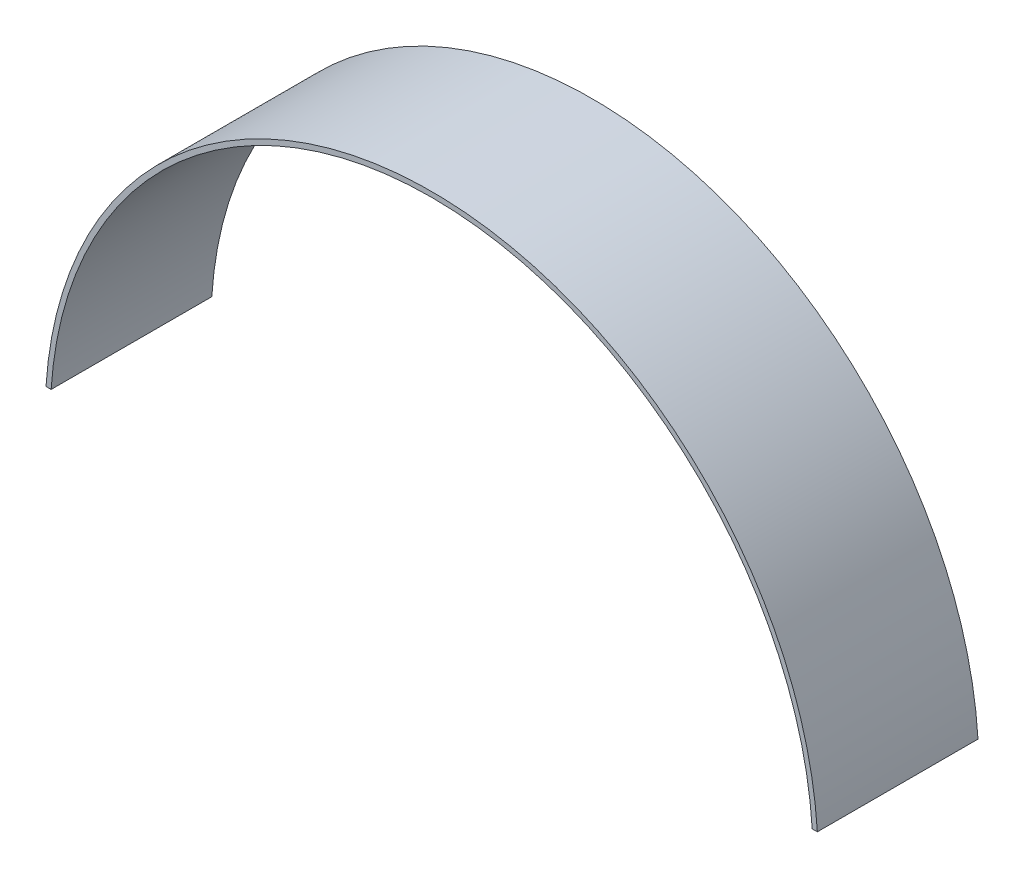
SolidWorks part; units mm, degrees
ref_plane "Front Plane" through (0, 0, 0) normal (0, 0, 1) x (1, 0, 0)
ref_plane "Top Plane" through (0, 0, 0) normal (0, 1, 0) x (1, 0, 0)
ref_plane "Right Plane" through (0, 0, 0) normal (1, 0, 0) x (0, 0, -1)
sketch "Sketch1" plane through (0, 0, 0) normal (0, 0, 1) x (1, 0, 0)
  line L1 (-90.1815, 4.6108) -> (-72.285, 4.6108)
  line L2 (-72.285, 4.6108) -> (-71.0625, 4.6108)
  line L3 (71.0625, 4.6108) -> (90.1815, 4.6108)
  arc A0 (90.1815, 4.6108) -> (-90.1815, 4.6108) centre (0, 0) ccw
  arc A1 (71.0625, 4.6108) -> (-71.0625, 4.6108) centre (0, 0) ccw
  arc A2 (72.0188, 4.6108) -> (-72.0188, 4.6108) centre (0, 0) ccw
  point P5 (0, 0)
extrude "Boss-Extrude1" add sketch "Sketch1" along normal blind 30 contours L3 A2 L2 A1
sketch3d "3DSketch1"
  line L0 (-72.0188, 4.6108, 15) -> (72.0188, 4.6108, 15)
  line L1 (-72.0188, 4.6108, 30) -> (-72.0188, 4.6108, 0) construction
  line L2 (72.0188, 4.6108, 30) -> (72.0188, 4.6108, 0) construction
  point P6 (-72.0188, 4.6108, 15)
  point P7 (0, 4.6108, 15)
  point P8 (72.0188, 4.6108, 15)
  point P9 (36.0188, 4.6108, 15)
  point P10 (-36.0188, 4.6108, 15)
  dimension "D5" = 144.0376
  dimension "D1" = 36
  dimension "D2" = 36
  dimension "D3" = 36.0188
  dimension "D4" = 36.0188
